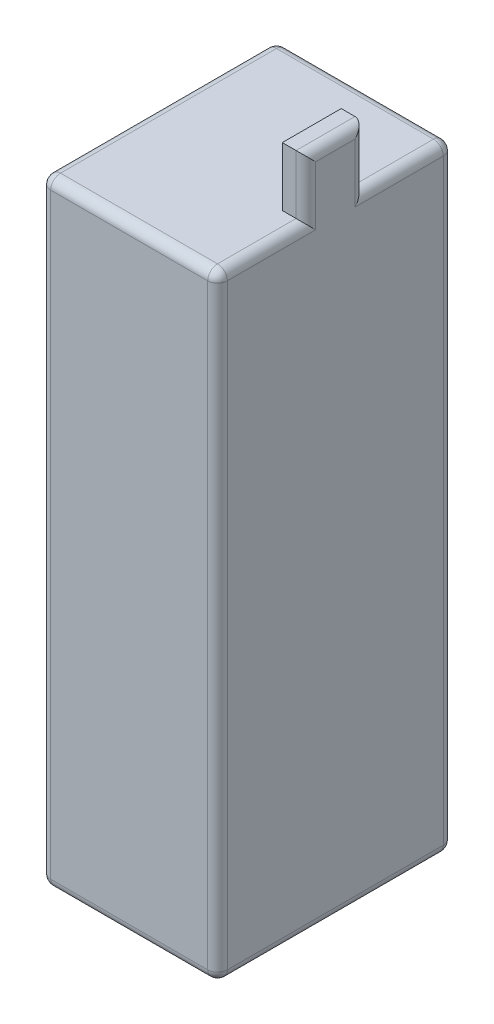
SolidWorks part; units mm, degrees
ref_plane "Front" through (0, 0, 0) normal (0, 0, 1) x (1, 0, 0)
ref_plane "Top" through (0, 0, 0) normal (0, 1, 0) x (1, 0, 0)
ref_plane "Right" through (0, 0, 0) normal (1, 0, 0) x (0, 0, -1)
sketch "Sketch1" plane through (0, 0, 0) normal (0, 1, 0) x (1, 0, 0)
  line L1 (0, 0) -> (45, 0)
  line L2 (0, 0) -> (0, 60)
  line L3 (0, 60) -> (45, 60)
  line L4 (45, 0) -> (45, 60)
  dimension "D1" = 45
  dimension "D2" = 60
extrude "Boss-Extrude1" add sketch "Sketch1" along normal blind 157
sketch "Sketch2" plane through (0, 157, 0) normal (0, 1, 0) x (1, 0, 0)
  line L0 (45, 0) -> (45, 60) construction
  line L1 (45, 22.5) -> (39, 22.5)
  line L2 (45, 22.5) -> (45, 37.5)
  line L3 (45, 37.5) -> (39, 37.5)
  line L4 (39, 22.5) -> (39, 37.5)
  line L5 (45, 30) -> (39, 30) construction
  line L6 (45, 60) -> (0, 60) construction
  line L7 (0, 0) -> (45, 0) construction
  dimension "D1" = 6
  dimension "D2" = 15
extrude "Boss-Extrude2" add sketch "Sketch2" along normal blind 15
fillet "Fillet1" radius 2.5 16 edges at (45, 157, -11.25) (45, 164.5, -22.5) (45, 172, -30) (45, 164.5, -37.5) (45, 157, -48.75) (45, 0, -30) (22.5, 157, 0) (45, 78.5, 0) (22.5, 0, 0) (0, 157, -30) (0, 78.5, 0) (0, 0, -30) (45, 78.5, -60) (22.5, 157, -60) (0, 78.5, -60) (22.5, 0, -60)
